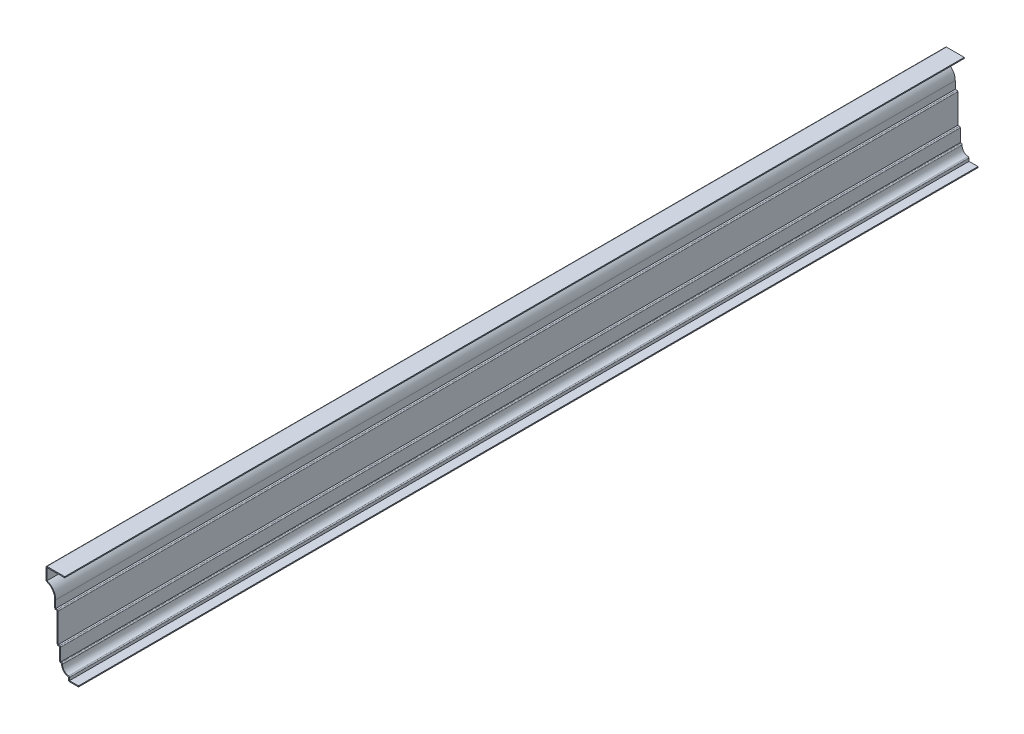
SolidWorks part; units mm, degrees
ref_plane "Front Plane" through (0, 0, 0) normal (0, 0, 1) x (1, 0, 0)
ref_plane "Top Plane" through (0, 0, 0) normal (0, 1, 0) x (1, 0, 0)
ref_plane "Right Plane" through (0, 0, 0) normal (1, 0, 0) x (0, 0, -1)
sketch "Sketch1" plane through (0, 0, 0) normal (0, 0, 1) x (1, 0, 0)
  line L0 (0, 0) -> (-12.7, 0)
  line L1 (-12.7, 0) -> (-12.7, 4.7625)
  line L2 (-21.4312, 15.0813) -> (-23.8125, 15.0813)
  line L3 (-23.8125, 15.0813) -> (-23.8125, 32.5438)
  line L4 (-23.8125, 32.5438) -> (-26.9875, 32.5438)
  line L5 (-26.9875, 32.5438) -> (-26.9875, 70.6438)
  line L6 (-26.9875, 70.6438) -> (-30.1625, 70.6438)
  line L7 (-30.1625, 70.6438) -> (-30.1625, 81.4941)
  line L8 (-41.275, 96.0438) -> (-41.275, 112.7125)
  line L9 (-41.275, 112.7125) -> (-17.4625, 112.7125)
  arc A0 (-12.7, 4.7625) -> (-21.4312, 15.0813) centre (-11.942, 14.2573) cw
  arc A1 (-30.1625, 81.4941) -> (-41.275, 96.0438) centre (-45.2437, 81.4941) ccw
  point P14 (0, 0)
  point P17 (0, 0)
  point P18 (-69.4578, 98.8487)
  dimension "D5" = 15.0812
  dimension "D13" = 9.525
  dimension "D1" = 112.7125
  dimension "D2" = 23.8125
  dimension "D3" = 16.6687
  dimension "D4" = 25.4
  dimension "D6" = 3.175
  dimension "D7" = 3.175
  dimension "D8" = 38.1
  dimension "D9" = 17.4625
  dimension "D10" = 10.3187
  dimension "D11" = 4.7625
  dimension "D12" = 12.7
  dimension "D14" = 8.7312
  dimension "D15" = 2.3813
  dimension "D16" = 41.275
extrude "Extrude-Thin1" add sketch "Sketch1" against normal blind 1143 thin
fillet "Fillet1" radius 1.27 10 edges at (-12.7, 0, -571.5) (-11.43, 6.0182, -571.5) (-19.927, 16.3513, -571.5) (-23.8125, 15.0813, -571.5) (-26.9875, 32.5438, -571.5) (-22.5425, 33.8138, -571.5) (-25.7175, 71.9137, -571.5) (-30.1625, 70.6438, -571.5) (-41.275, 96.0438, -571.5) (-41.275, 112.7125, -571.5)
